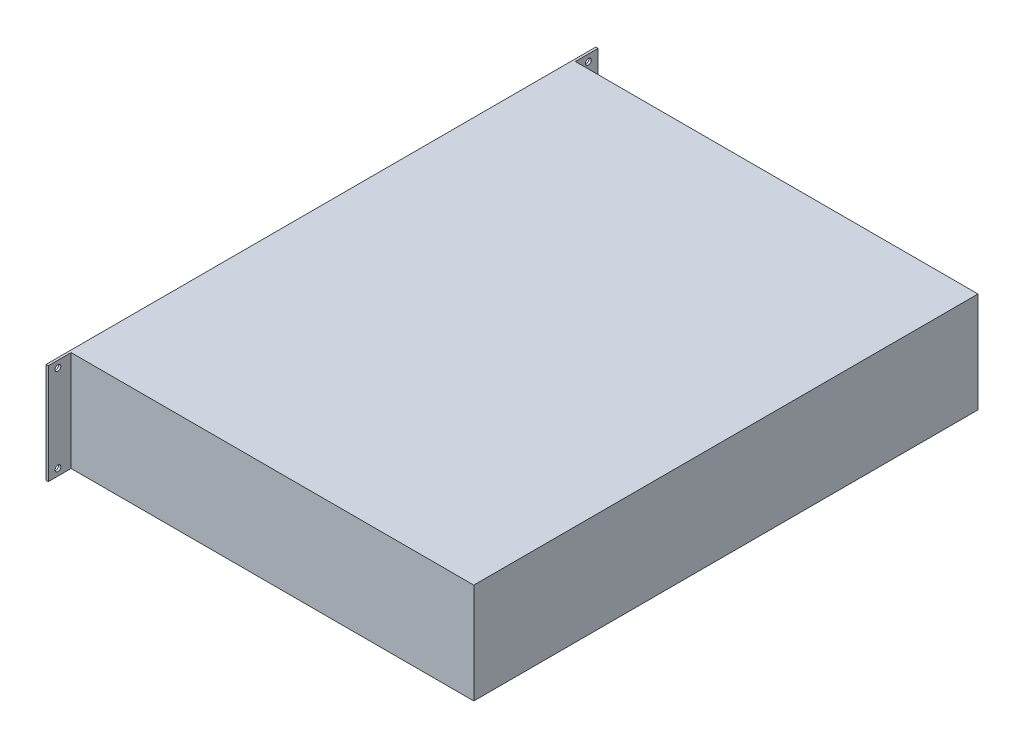
SolidWorks part; units mm, degrees
ref_plane "Alzado" through (0, 0, 0) normal (0, 0, 1) x (1, 0, 0)
ref_plane "Planta" through (0, 0, 0) normal (0, 1, 0) x (1, 0, 0)
ref_plane "Vista lateral" through (0, 0, 0) normal (1, 0, 0) x (0, 0, -1)
sketch "Croquis1" plane through (0, 0, 0) normal (0, 1, 0) x (1, 0, 0)
  line L1 (-177.5, 221) -> (177.5, 221)
  line L2 (-177.5, 221) -> (-177.5, -221)
  line L3 (-177.5, -221) -> (177.5, -221)
  line L4 (177.5, 221) -> (177.5, -221)
  line L5 (-177.5, 221) -> (177.5, -221) construction
  line L6 (-177.5, -221) -> (177.5, 221) construction
  point P0 (0, 0)
  dimension "D1" = 355
  dimension "D2" = 442
extrude "Saliente-Extruir1" add sketch "Croquis1" along normal blind 88
sketch "Croquis2" plane through (-177.5, 0, 0) normal (-1, 0, 0) x (0, 0, 1)
  line L0 (0, 44) -> (50000, 44) construction
  line L1 (-241, 88) -> (241, 88)
  line L2 (-241, 88) -> (-241, 0)
  line L3 (-241, 0) -> (241, 0)
  line L4 (241, 88) -> (241, 0)
  line L5 (-241, 88) -> (241, 0) construction
  line L6 (-241, 0) -> (241, 88) construction
  line L7 (0, 44) -> (0, 50044) construction
  line L8 (-221, 88) -> (-221, 0) construction
  circle A0 centre (232.5, 82.1) radius 2.5
  circle A1 centre (232.5, 5.9) radius 2.5
  circle A2 centre (-232.5, 5.9) radius 2.5
  circle A3 centre (-232.5, 82.1) radius 2.5
  point P0 (0, 44)
  point P12 (0, 0)
  point P15 (-221, 44)
  dimension "D4" = 5
  dimension "D1" = 482
  dimension "D2" = 76.2
  dimension "D3" = 465
extrude "Saliente-Extruir2" add sketch "Croquis2" against normal blind 2
